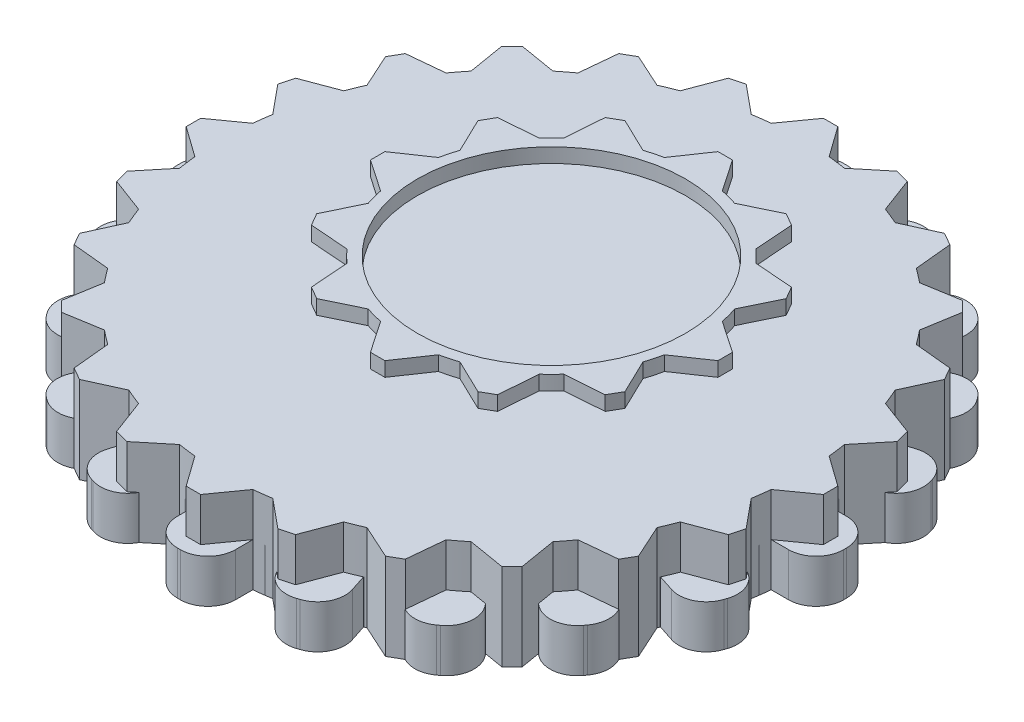
SolidWorks part; units mm, degrees
ref_plane "Front Plane" through (0, 0, 0) normal (0, 0, 1) x (1, 0, 0)
ref_plane "Top Plane" through (0, 0, 0) normal (0, 1, 0) x (1, 0, 0)
ref_plane "Right Plane" through (0, 0, 0) normal (1, 0, 0) x (0, 0, -1)
sketch "Sketch1" plane through (0, 0, 0) normal (0, 1, 0) x (1, 0, 0)
  line L86 (-2.6424, 4.8669) -> (1.3576, 4.8669)
  line L111 (-1.1424, 15.3669) -> (-0.1424, 15.3669)
  line L112 (-0.1424, 15.3669) -> (1.3576, 13.1649)
  line L113 (-1.1424, 15.3669) -> (-2.6424, 13.1649)
  line L114 (5.7906, 13.5092) -> (5.9886, 10.8522)
  line L115 (4.9246, 14.0092) -> (5.7906, 13.5092)
  line L116 (4.9246, 14.0092) -> (2.5245, 12.8522)
  line L117 (9.9999, 8.9339) -> (8.8429, 6.5338)
  line L118 (9.4999, 9.7999) -> (9.9999, 8.9339)
  line L119 (9.4999, 9.7999) -> (6.8429, 9.9979)
  line L120 (11.3576, 2.8669) -> (9.1556, 1.3669)
  line L121 (11.3576, 3.8669) -> (11.3576, 2.8669)
  line L122 (11.3576, 3.8669) -> (9.1556, 5.3669)
  line L123 (9.4999, -3.0661) -> (6.8429, -3.2641)
  line L124 (9.9999, -2.2001) -> (9.4999, -3.0661)
  line L125 (9.9999, -2.2001) -> (8.8429, 0.2)
  line L126 (4.9246, -7.2754) -> (2.5245, -6.1184)
  line L127 (5.7906, -6.7754) -> (4.9246, -7.2754)
  line L128 (5.7906, -6.7754) -> (5.9886, -4.1184)
  line L129 (-1.1424, -8.6331) -> (-2.6424, -6.4311)
  line L130 (-0.1424, -8.6331) -> (-1.1424, -8.6331)
  line L131 (-0.1424, -8.6331) -> (1.3576, -6.4311)
  line L132 (-7.0754, -6.7754) -> (-7.2734, -4.1184)
  line L133 (-6.2094, -7.2754) -> (-7.0754, -6.7754)
  line L134 (-6.2094, -7.2754) -> (-3.8093, -6.1184)
  line L135 (-11.2847, -2.2001) -> (-10.1277, 0.2)
  line L136 (-10.7847, -3.0661) -> (-11.2847, -2.2001)
  line L137 (-10.7847, -3.0661) -> (-8.1277, -3.2641)
  line L138 (-12.6424, 3.8669) -> (-10.4404, 5.3669)
  line L139 (-12.6424, 2.8669) -> (-12.6424, 3.8669)
  line L140 (-12.6424, 2.8669) -> (-10.4404, 1.3669)
  line L141 (-10.7847, 9.7999) -> (-8.1277, 9.9979)
  line L142 (-11.2847, 8.9339) -> (-10.7847, 9.7999)
  line L143 (-11.2847, 8.9339) -> (-10.1277, 6.5338)
  line L144 (-6.2094, 14.0092) -> (-3.8093, 12.8522)
  line L145 (-7.0754, 13.5092) -> (-6.2094, 14.0092)
  line L146 (-7.0754, 13.5092) -> (-7.2734, 10.8522)
  line L147 (-2.6424, 1.8669) -> (1.3576, 1.8669)
  line L149 (-3.1424, 4.8669) -> (1.8576, 1.8669) construction
  line L150 (-3.1424, 1.8669) -> (1.8576, 4.8669) construction
  arc A43 (-2.6424, 13.1649) -> (-3.8093, 12.8522) centre (-0.6424, 3.3669) ccw
  arc A44 (-7.2734, 10.8522) -> (-8.1277, 9.9979) centre (-0.6424, 3.3669) ccw
  arc A45 (-10.1277, 6.5338) -> (-10.4404, 5.3669) centre (-0.6424, 3.3669) ccw
  arc A46 (-10.4404, 1.3669) -> (-10.1277, 0.2) centre (-0.6424, 3.3669) ccw
  arc A47 (-8.1277, -3.2641) -> (-7.2734, -4.1184) centre (-0.6424, 3.3669) ccw
  arc A48 (-3.8093, -6.1184) -> (-2.6424, -6.4311) centre (-0.6424, 3.3669) ccw
  arc A49 (1.3576, -6.4311) -> (2.5245, -6.1184) centre (-0.6424, 3.3669) ccw
  arc A50 (5.9886, -4.1184) -> (6.8429, -3.2641) centre (-0.6424, 3.3669) ccw
  arc A51 (8.8429, 0.2) -> (9.1556, 1.3669) centre (-0.6424, 3.3669) ccw
  arc A52 (9.1556, 5.3669) -> (8.8429, 6.5338) centre (-0.6424, 3.3669) ccw
  arc A53 (6.8429, 9.9979) -> (5.9886, 10.8522) centre (-0.6424, 3.3669) ccw
  arc A54 (2.5245, 12.8522) -> (1.3576, 13.1649) centre (-0.6424, 3.3669) ccw
  arc A55 (-2.6424, 4.8669) -> (-2.6424, 1.8669) centre (-0.6424, 3.3669) ccw
  arc A56 (1.3576, 1.8669) -> (1.3576, 4.8669) centre (-0.6424, 3.3669) ccw
  point P6 (0, 0)
  point P8 (0, 0)
  point P9 (0, 0)
  point P12 (0, 2.7462)
  point P17 (0, 0)
  point P18 (0, 2.7462)
  point P22 (-2.5, 0.7462)
  point P63 (0, 0)
  point P68 (0, 0)
  point P69 (-0.6424, 3.3669)
  point P119 (0, 0)
  dimension "D1" = 20
  dimension "D2" = 3
  dimension "D3" = 5
  dimension "D8" = 12
sketch "Sketch2" plane through (0, 0, 0) normal (0, 1, 0) x (1, 0, 0)
  line L0 (-2, 0) -> (2, 0)
  line L1 (-23, -0.1) -> (-23, 0.1)
  line L2 (-21.1, 2) -> (-19.8997, 2)
  line L3 (-21.1, -2) -> (-19.8997, -2)
  line L4 (-20.6853, 4.6181) -> (-19.5438, 4.2472)
  line L5 (-19.4493, 8.4224) -> (-18.3078, 8.0515)
  line L6 (-21.9052, 7.0123) -> (-21.8434, 7.2025)
  line L7 (-18.2458, 10.7842) -> (-17.2748, 10.0787)
  line L8 (-15.8947, 14.0203) -> (-14.9237, 13.3148)
  line L9 (-18.6662, 13.4382) -> (-18.5486, 13.6)
  line L10 (-14.0203, 15.8947) -> (-13.3148, 14.9237)
  line L11 (-10.7842, 18.2458) -> (-10.0787, 17.2748)
  line L12 (-13.6, 18.5486) -> (-13.4382, 18.6662)
  line L13 (-8.4224, 19.4493) -> (-8.0515, 18.3078)
  line L14 (-4.6181, 20.6853) -> (-4.2472, 19.5438)
  line L15 (-7.2025, 21.8434) -> (-7.0123, 21.9052)
  line L16 (-2, 21.1) -> (-2, 19.8997)
  line L17 (2, 21.1) -> (2, 19.8997)
  line L18 (-0.1, 23) -> (0.1, 23)
  line L19 (4.6181, 20.6853) -> (4.2472, 19.5438)
  line L20 (8.4224, 19.4493) -> (8.0515, 18.3078)
  line L21 (7.0123, 21.9052) -> (7.2025, 21.8434)
  line L22 (10.7842, 18.2458) -> (10.0787, 17.2748)
  line L23 (14.0203, 15.8947) -> (13.3148, 14.9237)
  line L24 (13.4382, 18.6662) -> (13.6, 18.5486)
  line L25 (15.8947, 14.0203) -> (14.9237, 13.3148)
  line L26 (18.2458, 10.7842) -> (17.2748, 10.0787)
  line L27 (18.5486, 13.6) -> (18.6662, 13.4382)
  line L28 (19.4493, 8.4224) -> (18.3078, 8.0515)
  line L29 (20.6853, 4.6181) -> (19.5438, 4.2472)
  line L30 (21.8434, 7.2025) -> (21.9052, 7.0123)
  line L31 (21.1, 2) -> (19.8997, 2)
  line L32 (21.1, -2) -> (19.8997, -2)
  line L33 (23, 0.1) -> (23, -0.1)
  line L34 (20.6853, -4.6181) -> (19.5438, -4.2472)
  line L35 (19.4493, -8.4224) -> (18.3078, -8.0515)
  line L36 (21.9052, -7.0123) -> (21.8434, -7.2025)
  line L37 (18.2458, -10.7842) -> (17.2748, -10.0787)
  line L38 (15.8947, -14.0203) -> (14.9237, -13.3148)
  line L39 (18.6662, -13.4382) -> (18.5486, -13.6)
  line L40 (14.0203, -15.8947) -> (13.3148, -14.9237)
  line L41 (10.7842, -18.2458) -> (10.0787, -17.2748)
  line L42 (13.6, -18.5486) -> (13.4382, -18.6662)
  line L43 (8.4224, -19.4493) -> (8.0515, -18.3078)
  line L44 (4.6181, -20.6853) -> (4.2472, -19.5438)
  line L45 (7.2025, -21.8434) -> (7.0123, -21.9052)
  line L46 (2, -21.1) -> (2, -19.8997)
  line L47 (-2, -21.1) -> (-2, -19.8997)
  line L48 (0.1, -23) -> (-0.1, -23)
  line L49 (-4.6181, -20.6853) -> (-4.2472, -19.5438)
  line L50 (-8.4224, -19.4493) -> (-8.0515, -18.3078)
  line L51 (-7.0123, -21.9052) -> (-7.2025, -21.8434)
  line L52 (-10.7842, -18.2458) -> (-10.0787, -17.2748)
  line L53 (-14.0203, -15.8947) -> (-13.3148, -14.9237)
  line L54 (-13.4382, -18.6662) -> (-13.6, -18.5486)
  line L55 (-15.8947, -14.0203) -> (-14.9237, -13.3148)
  line L56 (-18.2458, -10.7842) -> (-17.2748, -10.0787)
  line L57 (-18.5486, -13.6) -> (-18.6662, -13.4382)
  line L58 (-19.4493, -8.4224) -> (-18.3078, -8.0515)
  line L59 (-20.6853, -4.6181) -> (-19.5438, -4.2472)
  line L60 (-21.8434, -7.2025) -> (-21.9052, -7.0123)
  arc A0 (-18.3078, -8.0515) -> (-17.2748, -10.0787) centre (0, 0) ccw
  arc A1 (-21.1, 2) -> (-23, 0.1) centre (-21.1, 0.1) ccw
  arc A2 (-21.1, -2) -> (-23, -0.1) centre (-21.1, -0.1) cw
  arc A3 (-20.6853, 4.6181) -> (-21.9052, 7.0123) centre (-20.0982, 6.4252) cw
  arc A4 (-19.4493, 8.4224) -> (-21.8434, 7.2025) centre (-20.0364, 6.6154) ccw
  arc A5 (-18.2458, 10.7842) -> (-18.6662, 13.4382) centre (-17.129, 12.3214) cw
  arc A6 (-15.8947, 14.0203) -> (-18.5486, 13.6) centre (-17.0115, 12.4832) ccw
  arc A7 (-14.0203, 15.8947) -> (-13.6, 18.5486) centre (-12.4832, 17.0115) cw
  arc A8 (-10.7842, 18.2458) -> (-13.4382, 18.6662) centre (-12.3214, 17.129) ccw
  arc A9 (-8.4224, 19.4493) -> (-7.2025, 21.8434) centre (-6.6154, 20.0364) cw
  arc A10 (-4.6181, 20.6853) -> (-7.0123, 21.9052) centre (-6.4252, 20.0982) ccw
  arc A11 (-2, 21.1) -> (-0.1, 23) centre (-0.1, 21.1) cw
  arc A12 (2, 21.1) -> (0.1, 23) centre (0.1, 21.1) ccw
  arc A13 (4.6181, 20.6853) -> (7.0123, 21.9052) centre (6.4252, 20.0982) cw
  arc A14 (8.4224, 19.4493) -> (7.2025, 21.8434) centre (6.6154, 20.0364) ccw
  arc A15 (10.7842, 18.2458) -> (13.4382, 18.6662) centre (12.3214, 17.129) cw
  arc A16 (14.0203, 15.8947) -> (13.6, 18.5486) centre (12.4832, 17.0115) ccw
  arc A17 (15.8947, 14.0203) -> (18.5486, 13.6) centre (17.0115, 12.4832) cw
  arc A18 (18.2458, 10.7842) -> (18.6662, 13.4382) centre (17.129, 12.3214) ccw
  arc A19 (19.4493, 8.4224) -> (21.8434, 7.2025) centre (20.0364, 6.6154) cw
  arc A20 (20.6853, 4.6181) -> (21.9052, 7.0123) centre (20.0982, 6.4252) ccw
  arc A21 (21.1, 2) -> (23, 0.1) centre (21.1, 0.1) cw
  arc A22 (21.1, -2) -> (23, -0.1) centre (21.1, -0.1) ccw
  arc A23 (20.6853, -4.6181) -> (21.9052, -7.0123) centre (20.0982, -6.4252) cw
  arc A24 (19.4493, -8.4224) -> (21.8434, -7.2025) centre (20.0364, -6.6154) ccw
  arc A25 (18.2458, -10.7842) -> (18.6662, -13.4382) centre (17.129, -12.3214) cw
  arc A26 (15.8947, -14.0203) -> (18.5486, -13.6) centre (17.0115, -12.4832) ccw
  arc A27 (14.0203, -15.8947) -> (13.6, -18.5486) centre (12.4832, -17.0115) cw
  arc A28 (10.7842, -18.2458) -> (13.4382, -18.6662) centre (12.3214, -17.129) ccw
  arc A29 (8.4224, -19.4493) -> (7.2025, -21.8434) centre (6.6154, -20.0364) cw
  arc A30 (4.6181, -20.6853) -> (7.0123, -21.9052) centre (6.4252, -20.0982) ccw
  arc A31 (2, -21.1) -> (0.1, -23) centre (0.1, -21.1) cw
  arc A32 (-2, -21.1) -> (-0.1, -23) centre (-0.1, -21.1) ccw
  arc A33 (-4.6181, -20.6853) -> (-7.0123, -21.9052) centre (-6.4252, -20.0982) cw
  arc A34 (-8.4224, -19.4493) -> (-7.2025, -21.8434) centre (-6.6154, -20.0364) ccw
  arc A35 (-10.7842, -18.2458) -> (-13.4382, -18.6662) centre (-12.3214, -17.129) cw
  arc A36 (-14.0203, -15.8947) -> (-13.6, -18.5486) centre (-12.4832, -17.0115) ccw
  arc A37 (-15.8947, -14.0203) -> (-18.5486, -13.6) centre (-17.0115, -12.4832) cw
  arc A38 (-18.2458, -10.7842) -> (-18.6662, -13.4382) centre (-17.129, -12.3214) ccw
  arc A39 (-19.4493, -8.4224) -> (-21.8434, -7.2025) centre (-20.0364, -6.6154) cw
  arc A40 (-20.6853, -4.6181) -> (-21.9052, -7.0123) centre (-20.0982, -6.4252) ccw
  arc A41 (-19.8997, -2) -> (-19.5438, -4.2472) centre (0, 0) ccw
  arc A42 (-19.5438, 4.2472) -> (-19.8997, 2) centre (0, 0) ccw
  arc A43 (-17.2748, 10.0787) -> (-18.3078, 8.0515) centre (0, 0) ccw
  arc A44 (-13.3148, 14.9237) -> (-14.9237, 13.3148) centre (0, 0) ccw
  arc A45 (-8.0515, 18.3078) -> (-10.0787, 17.2748) centre (0, 0) ccw
  arc A46 (-2, 19.8997) -> (-4.2472, 19.5438) centre (0, 0) ccw
  arc A47 (4.2472, 19.5438) -> (2, 19.8997) centre (0, 0) ccw
  arc A48 (10.0787, 17.2748) -> (8.0515, 18.3078) centre (0, 0) ccw
  arc A49 (14.9237, 13.3148) -> (13.3148, 14.9237) centre (0, 0) ccw
  arc A50 (18.3078, 8.0515) -> (17.2748, 10.0787) centre (0, 0) ccw
  arc A51 (19.8997, 2) -> (19.5438, 4.2472) centre (0, 0) ccw
  arc A52 (19.5438, -4.2472) -> (19.8997, -2) centre (0, 0) ccw
  arc A53 (17.2748, -10.0787) -> (18.3078, -8.0515) centre (0, 0) ccw
  arc A54 (13.3148, -14.9237) -> (14.9237, -13.3148) centre (0, 0) ccw
  arc A55 (8.0515, -18.3078) -> (10.0787, -17.2748) centre (0, 0) ccw
  arc A56 (2, -19.8997) -> (4.2472, -19.5438) centre (0, 0) ccw
  arc A57 (-10.0787, -17.2748) -> (-8.0515, -18.3078) centre (0, 0) ccw
  arc A58 (-4.2472, -19.5438) -> (-2, -19.8997) centre (0, 0) ccw
  arc A59 (-14.9237, -13.3148) -> (-13.3148, -14.9237) centre (0, 0) ccw
  point P6 (0, 0)
  point P10 (-23, 2)
  point P170 (0, 0)
  dimension "D1" = 40
  dimension "D4" = 1.9
  dimension "D5" = 20
extrude "Boss-Extrude3" add sketch "Sketch2" along normal blind 3
sketch "Sketch3" plane through (0, 0, 0) normal (0, 1, 0) x (1, 0, 0)
  line L0 (-22, 0) -> (22, 0)
  line L1 (22, -0.5) -> (22, 0.5)
  line L2 (22, 0.5) -> (19.8997, 2)
  line L3 (22, -0.5) -> (19.8997, -2)
  line L4 (21.3798, -5.2111) -> (19.7393, -3.2186)
  line L5 (21.121, -6.177) -> (21.3798, -5.2111)
  line L6 (21.121, -6.177) -> (18.704, -7.0823)
  line L7 (19.3026, -10.567) -> (18.2337, -8.2178)
  line L8 (18.8026, -11.433) -> (19.3026, -10.567)
  line L9 (18.8026, -11.433) -> (16.2337, -11.6819)
  line L10 (15.9099, -15.2028) -> (15.4855, -12.657)
  line L11 (15.2028, -15.9099) -> (15.9099, -15.2028)
  line L12 (15.2028, -15.9099) -> (12.657, -15.4855)
  line L13 (11.433, -18.8026) -> (11.6819, -16.2337)
  line L14 (10.567, -19.3026) -> (11.433, -18.8026)
  line L15 (10.567, -19.3026) -> (8.2178, -18.2337)
  line L16 (6.177, -21.121) -> (7.0823, -18.704)
  line L17 (5.2111, -21.3798) -> (6.177, -21.121)
  line L18 (5.2111, -21.3798) -> (3.2186, -19.7393)
  line L19 (0.5, -22) -> (2, -19.8997)
  line L20 (-0.5, -22) -> (0.5, -22)
  line L21 (-0.5, -22) -> (-2, -19.8997)
  line L22 (-5.2111, -21.3798) -> (-3.2186, -19.7393)
  line L23 (-6.177, -21.121) -> (-5.2111, -21.3798)
  line L24 (-6.177, -21.121) -> (-7.0823, -18.704)
  line L25 (-10.567, -19.3026) -> (-8.2178, -18.2337)
  line L26 (-11.433, -18.8026) -> (-10.567, -19.3026)
  line L27 (-11.433, -18.8026) -> (-11.6819, -16.2337)
  line L28 (-15.2028, -15.9099) -> (-12.657, -15.4855)
  line L29 (-15.9099, -15.2028) -> (-15.2028, -15.9099)
  line L30 (-15.9099, -15.2028) -> (-15.4855, -12.657)
  line L31 (-18.8026, -11.433) -> (-16.2337, -11.6819)
  line L32 (-19.3026, -10.567) -> (-18.8026, -11.433)
  line L33 (-19.3026, -10.567) -> (-18.2337, -8.2178)
  line L34 (-21.121, -6.177) -> (-18.704, -7.0823)
  line L35 (-21.3798, -5.2111) -> (-21.121, -6.177)
  line L36 (-21.3798, -5.2111) -> (-19.7393, -3.2186)
  line L37 (-22, -0.5) -> (-19.8997, -2)
  line L38 (-22, 0.5) -> (-22, -0.5)
  line L39 (-22, 0.5) -> (-19.8997, 2)
  line L40 (-21.3798, 5.2111) -> (-19.7393, 3.2186)
  line L41 (-21.121, 6.177) -> (-21.3798, 5.2111)
  line L42 (-21.121, 6.177) -> (-18.704, 7.0823)
  line L43 (-19.3026, 10.567) -> (-18.2337, 8.2178)
  line L44 (-18.8026, 11.433) -> (-19.3026, 10.567)
  line L45 (-18.8026, 11.433) -> (-16.2337, 11.6819)
  line L46 (-15.9099, 15.2028) -> (-15.4855, 12.657)
  line L47 (-15.2028, 15.9099) -> (-15.9099, 15.2028)
  line L48 (-15.2028, 15.9099) -> (-12.657, 15.4855)
  line L49 (-11.433, 18.8026) -> (-11.6819, 16.2337)
  line L50 (-10.567, 19.3026) -> (-11.433, 18.8026)
  line L51 (-10.567, 19.3026) -> (-8.2178, 18.2337)
  line L52 (-6.177, 21.121) -> (-7.0823, 18.704)
  line L53 (-5.2111, 21.3798) -> (-6.177, 21.121)
  line L54 (-5.2111, 21.3798) -> (-3.2186, 19.7393)
  line L55 (-0.5, 22) -> (-2, 19.8997)
  line L56 (0.5, 22) -> (-0.5, 22)
  line L57 (0.5, 22) -> (2, 19.8997)
  line L58 (5.2111, 21.3798) -> (3.2186, 19.7393)
  line L59 (6.177, 21.121) -> (5.2111, 21.3798)
  line L60 (6.177, 21.121) -> (7.0823, 18.704)
  line L61 (10.567, 19.3026) -> (8.2178, 18.2337)
  line L62 (11.433, 18.8026) -> (10.567, 19.3026)
  line L63 (11.433, 18.8026) -> (11.6819, 16.2337)
  line L64 (15.2028, 15.9099) -> (12.657, 15.4855)
  line L65 (15.9099, 15.2028) -> (15.2028, 15.9099)
  line L66 (15.9099, 15.2028) -> (15.4855, 12.657)
  line L67 (18.8026, 11.433) -> (16.2337, 11.6819)
  line L68 (19.3026, 10.567) -> (18.8026, 11.433)
  line L69 (19.3026, 10.567) -> (18.2337, 8.2178)
  line L70 (21.121, 6.177) -> (18.704, 7.0823)
  line L71 (21.3798, 5.2111) -> (21.121, 6.177)
  line L72 (21.3798, 5.2111) -> (19.7393, 3.2186)
  arc A0 (-8.2178, -18.2337) -> (-7.0823, -18.704) centre (0, 0) ccw
  arc A1 (-12.657, -15.4855) -> (-11.6819, -16.2337) centre (0, 0) ccw
  arc A2 (-16.2337, -11.6819) -> (-15.4855, -12.657) centre (0, 0) ccw
  arc A3 (-18.704, -7.0823) -> (-18.2337, -8.2178) centre (0, 0) ccw
  arc A4 (-19.8997, -2) -> (-19.7393, -3.2186) centre (0, 0) ccw
  arc A5 (-19.7393, 3.2186) -> (-19.8997, 2) centre (0, 0) ccw
  arc A6 (-18.2337, 8.2178) -> (-18.704, 7.0823) centre (0, 0) ccw
  arc A7 (-15.4855, 12.657) -> (-16.2337, 11.6819) centre (0, 0) ccw
  arc A8 (-11.6819, 16.2337) -> (-12.657, 15.4855) centre (0, 0) ccw
  arc A9 (-7.0823, 18.704) -> (-8.2178, 18.2337) centre (0, 0) ccw
  arc A10 (-2, 19.8997) -> (-3.2186, 19.7393) centre (0, 0) ccw
  arc A11 (3.2186, 19.7393) -> (2, 19.8997) centre (0, 0) ccw
  arc A12 (8.2178, 18.2337) -> (7.0823, 18.704) centre (0, 0) ccw
  arc A13 (12.657, 15.4855) -> (11.6819, 16.2337) centre (0, 0) ccw
  arc A14 (16.2337, 11.6819) -> (15.4855, 12.657) centre (0, 0) ccw
  arc A15 (18.704, 7.0823) -> (18.2337, 8.2178) centre (0, 0) ccw
  arc A16 (19.8997, 2) -> (19.7393, 3.2186) centre (0, 0) ccw
  arc A17 (19.7393, -3.2186) -> (19.8997, -2) centre (0, 0) ccw
  arc A18 (18.2337, -8.2178) -> (18.704, -7.0823) centre (0, 0) ccw
  arc A19 (-3.2186, -19.7393) -> (-2, -19.8997) centre (0, 0) ccw
  arc A20 (2, -19.8997) -> (3.2186, -19.7393) centre (0, 0) ccw
  arc A21 (7.0823, -18.704) -> (8.2178, -18.2337) centre (0, 0) ccw
  arc A22 (11.6819, -16.2337) -> (12.657, -15.4855) centre (0, 0) ccw
  arc A23 (15.4855, -12.657) -> (16.2337, -11.6819) centre (0, 0) ccw
  point P6 (0, 0)
  point P7 (0, -12.952)
  point P8 (-6.2727, 0)
  point P9 (11.4668, 0)
  point P10 (0, 0)
  point P108 (0, 0)
  dimension "D1" = 40
  dimension "D2" = 22
  dimension "D3" = 2
  dimension "D4" = 24
extrude "Boss-Extrude5" add sketch "Sketch3" along normal blind 6 separate body contours L2 A16 L72 L71 L70 A15 L69 L68 L67 A14 L66 L65 L64 A13 L63 L62 L61 A12 L60 L59 L58 A11 L57 L56 L55 A10 L54 L53 L52 A9 L51 L50 L49 A8 L48 L47 L46 A7 L45 L44 L43 A6 L42 L41 L40 A5 L39 L38 L0 L1 | L10 A23 L9 L8 L7 A18 L6 L5 L4 A17 L3 L1 L0 L38 L37 A4 L36 L35 L34 A3 L33 L32 L31 A2 L30 L29 L28 A1 L27 L26 L25 A0 L24 L23 L22 A19 L21 L20 L19 A20 L18 L17 L16 A21 L15 L14 L13 A22 L12 L11
extrude "Boss-Extrude6" add sketch "Sketch1" along normal blind 5.5 separate body
sketch "Sketch5" plane through (0, 5.5, 0) normal (0, 1, 0) x (1, 0, 0)
  line L0 (-0.6424, 15.3669) -> (-0.6424, -8.6331) construction
  line L1 (-0.1424, 15.3669) -> (-1.1424, 15.3669) construction
  line L2 (-1.1424, -8.6331) -> (-0.1424, -8.6331) construction
  line L3 (11.3576, 3.3669) -> (-12.6424, 3.3669) construction
  line L4 (11.3576, 2.8669) -> (11.3576, 3.8669) construction
  line L5 (-12.6424, 3.8669) -> (-12.6424, 2.8669) construction
  circle A0 centre (-0.6424, 3.3669) radius 5.1751
sketch "Sketch6" plane through (0, 5.5, 0) normal (0, 1, 0) x (1, 0, 0)
  line L72 (-1.1424, 15.3669) -> (-2.6424, 13.1649)
  line L73 (-3.8093, 12.8522) -> (-6.2094, 14.0092)
  line L74 (-6.2094, 14.0092) -> (-7.0754, 13.5092)
  line L75 (-7.0754, 13.5092) -> (-7.2734, 10.8522)
  line L76 (-8.1277, 9.9979) -> (-10.7847, 9.7999)
  line L77 (-10.7847, 9.7999) -> (-11.2847, 8.9339)
  line L78 (-11.2847, 8.9339) -> (-10.1277, 6.5338)
  line L79 (-10.4404, 5.3669) -> (-12.6424, 3.8669)
  line L80 (-12.6424, 3.8669) -> (-12.6424, 2.8669)
  line L81 (-12.6424, 2.8669) -> (-10.4404, 1.3669)
  line L82 (-10.1277, 0.2) -> (-11.2847, -2.2001)
  line L83 (-11.2847, -2.2001) -> (-10.7847, -3.0661)
  line L84 (-10.7847, -3.0661) -> (-8.1277, -3.2641)
  line L85 (-7.2734, -4.1184) -> (-7.0754, -6.7754)
  line L86 (-7.0754, -6.7754) -> (-6.2094, -7.2754)
  line L87 (-6.2094, -7.2754) -> (-3.8093, -6.1184)
  line L88 (-2.6424, -6.4311) -> (-1.1424, -8.6331)
  line L89 (-1.1424, -8.6331) -> (-0.1424, -8.6331)
  line L90 (-0.1424, -8.6331) -> (1.3576, -6.4311)
  line L91 (2.5245, -6.1184) -> (4.9246, -7.2754)
  line L92 (4.9246, -7.2754) -> (5.7906, -6.7754)
  line L93 (5.7906, -6.7754) -> (5.9886, -4.1184)
  line L94 (6.8429, -3.2641) -> (9.4999, -3.0661)
  line L95 (9.4999, -3.0661) -> (9.9999, -2.2001)
  line L96 (9.9999, -2.2001) -> (8.8429, 0.2)
  line L97 (9.1556, 1.3669) -> (11.3576, 2.8669)
  line L98 (11.3576, 2.8669) -> (11.3576, 3.8669)
  line L99 (11.3576, 3.8669) -> (9.1556, 5.3669)
  line L100 (8.8429, 6.5338) -> (9.9999, 8.9339)
  line L101 (9.9999, 8.9339) -> (9.4999, 9.7999)
  line L102 (9.4999, 9.7999) -> (6.8429, 9.9979)
  line L103 (5.9886, 10.8522) -> (5.7906, 13.5092)
  line L104 (5.7906, 13.5092) -> (4.9246, 14.0092)
  line L105 (4.9246, 14.0092) -> (2.5245, 12.8522)
  line L106 (1.3576, 13.1649) -> (-0.1424, 15.3669)
  line L107 (-0.1424, 15.3669) -> (-1.1424, 15.3669)
  line L108 (-1.1424, 15.3669) -> (-2.6424, 13.1649)
  line L109 (-3.8093, 12.8522) -> (-6.2094, 14.0092)
  line L110 (-6.2094, 14.0092) -> (-7.0754, 13.5092)
  line L111 (-7.0754, 13.5092) -> (-7.2734, 10.8522)
  line L112 (-8.1277, 9.9979) -> (-10.7847, 9.7999)
  line L113 (-10.7847, 9.7999) -> (-11.2847, 8.9339)
  line L114 (-11.2847, 8.9339) -> (-10.1277, 6.5338)
  line L115 (-10.4404, 5.3669) -> (-12.6424, 3.8669)
  line L116 (-12.6424, 3.8669) -> (-12.6424, 2.8669)
  line L117 (-12.6424, 2.8669) -> (-10.4404, 1.3669)
  line L118 (-10.1277, 0.2) -> (-11.2847, -2.2001)
  line L119 (-11.2847, -2.2001) -> (-10.7847, -3.0661)
  line L120 (-10.7847, -3.0661) -> (-8.1277, -3.2641)
  line L121 (-7.2734, -4.1184) -> (-7.0754, -6.7754)
  line L122 (-7.0754, -6.7754) -> (-6.2094, -7.2754)
  line L123 (-6.2094, -7.2754) -> (-3.8093, -6.1184)
  line L124 (-2.6424, -6.4311) -> (-1.1424, -8.6331)
  line L125 (-1.1424, -8.6331) -> (-0.1424, -8.6331)
  line L126 (-0.1424, -8.6331) -> (1.3576, -6.4311)
  line L127 (2.5245, -6.1184) -> (4.9246, -7.2754)
  line L128 (4.9246, -7.2754) -> (5.7906, -6.7754)
  line L129 (5.7906, -6.7754) -> (5.9886, -4.1184)
  line L130 (6.8429, -3.2641) -> (9.4999, -3.0661)
  line L131 (9.4999, -3.0661) -> (9.9999, -2.2001)
  line L132 (9.9999, -2.2001) -> (8.8429, 0.2)
  line L133 (9.1556, 1.3669) -> (11.3576, 2.8669)
  line L134 (11.3576, 2.8669) -> (11.3576, 3.8669)
  line L135 (11.3576, 3.8669) -> (9.1556, 5.3669)
  line L136 (8.8429, 6.5338) -> (9.9999, 8.9339)
  line L137 (9.9999, 8.9339) -> (9.4999, 9.7999)
  line L138 (9.4999, 9.7999) -> (6.8429, 9.9979)
  line L139 (5.9886, 10.8522) -> (5.7906, 13.5092)
  line L140 (5.7906, 13.5092) -> (4.9246, 14.0092)
  line L141 (4.9246, 14.0092) -> (2.5245, 12.8522)
  line L142 (1.3576, 13.1649) -> (-0.1424, 15.3669)
  line L143 (-0.1424, 15.3669) -> (-1.1424, 15.3669)
  circle A0 centre (-0.6424, 3.3669) radius 9.25
  arc A27 (-2.6424, 13.1649) -> (-3.8093, 12.8522) centre (-0.6424, 3.3669) ccw
  arc A28 (-7.2734, 10.8522) -> (-8.1277, 9.9979) centre (-0.6424, 3.3669) ccw
  arc A29 (-10.1277, 6.5338) -> (-10.4404, 5.3669) centre (-0.6424, 3.3669) ccw
  arc A30 (-10.4404, 1.3669) -> (-10.1277, 0.2) centre (-0.6424, 3.3669) ccw
  arc A31 (-8.1277, -3.2641) -> (-7.2734, -4.1184) centre (-0.6424, 3.3669) ccw
  arc A32 (-3.8093, -6.1184) -> (-2.6424, -6.4311) centre (-0.6424, 3.3669) ccw
  arc A33 (1.3576, -6.4311) -> (2.5245, -6.1184) centre (-0.6424, 3.3669) ccw
  arc A34 (5.9886, -4.1184) -> (6.8429, -3.2641) centre (-0.6424, 3.3669) ccw
  arc A35 (8.8429, 0.2) -> (9.1556, 1.3669) centre (-0.6424, 3.3669) ccw
  arc A36 (9.1556, 5.3669) -> (8.8429, 6.5338) centre (-0.6424, 3.3669) ccw
  arc A37 (6.8429, 9.9979) -> (5.9886, 10.8522) centre (-0.6424, 3.3669) ccw
  arc A38 (2.5245, 12.8522) -> (1.3576, 13.1649) centre (-0.6424, 3.3669) ccw
  arc A39 (-2.6424, 13.1649) -> (-3.8093, 12.8522) centre (-0.6424, 3.3669) ccw
  arc A40 (-7.2734, 10.8522) -> (-8.1277, 9.9979) centre (-0.6424, 3.3669) ccw
  arc A41 (-10.1277, 6.5338) -> (-10.4404, 5.3669) centre (-0.6424, 3.3669) ccw
  arc A42 (-10.4404, 1.3669) -> (-10.1277, 0.2) centre (-0.6424, 3.3669) ccw
  arc A43 (-8.1277, -3.2641) -> (-7.2734, -4.1184) centre (-0.6424, 3.3669) ccw
  arc A44 (-3.8093, -6.1184) -> (-2.6424, -6.4311) centre (-0.6424, 3.3669) ccw
  arc A45 (1.3576, -6.4311) -> (2.5245, -6.1184) centre (-0.6424, 3.3669) ccw
  arc A46 (5.9886, -4.1184) -> (6.8429, -3.2641) centre (-0.6424, 3.3669) ccw
  arc A47 (8.8429, 0.2) -> (9.1556, 1.3669) centre (-0.6424, 3.3669) ccw
  arc A48 (9.1556, 5.3669) -> (8.8429, 6.5338) centre (-0.6424, 3.3669) ccw
  arc A49 (6.8429, 9.9979) -> (5.9886, 10.8522) centre (-0.6424, 3.3669) ccw
  arc A50 (2.5245, 12.8522) -> (1.3576, 13.1649) centre (-0.6424, 3.3669) ccw
  dimension "D1" = 18.5
  dimension "D3" = 0
extrude "Boss-Extrude7" add sketch "Sketch6" along normal blind 1.5
